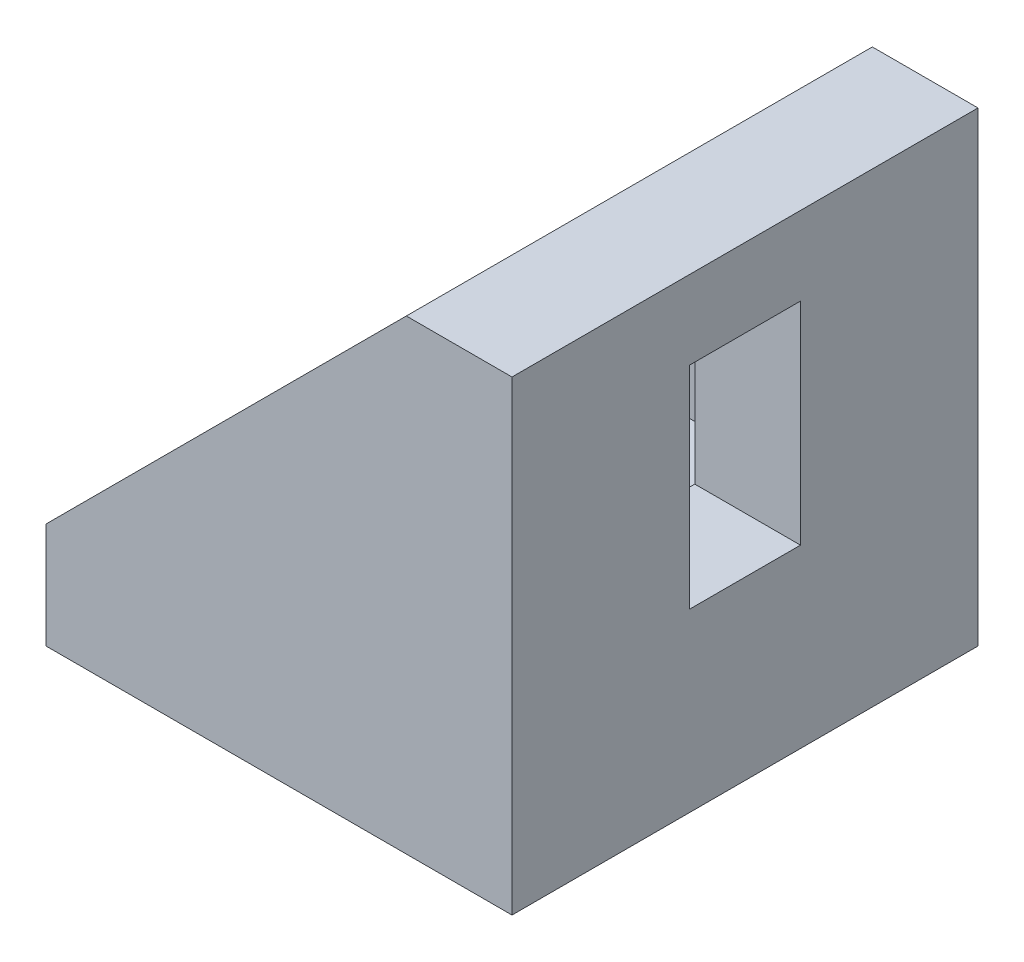
SolidWorks part; units mm, degrees
ref_plane "Front Plane" through (0, 0, 0) normal (0, 0, 1) x (1, 0, 0)
ref_plane "Top Plane" through (0, 0, 0) normal (0, 1, 0) x (1, 0, 0)
ref_plane "Right Plane" through (0, 0, 0) normal (1, 0, 0) x (0, 0, -1)
sketch "Sketch1" plane through (0, 0, 0) normal (0, 0, 1) x (1, 0, 0)
  line L0 (0, 0) -> (-42, 0)
  line L1 (-42, 0) -> (-42, 9.525)
  line L2 (-42, 9.525) -> (-9.525, 9.525)
  line L3 (-9.525, 9.525) -> (-9.525, 42)
  line L4 (-9.525, 42) -> (0, 42)
  line L5 (0, 42) -> (0, 0)
  dimension "D1" = 42
  dimension "D2" = 42
  dimension "D3" = 9.525
  dimension "D4" = 9.525
extrude "Boss-Extrude1" add sketch "Sketch1" along normal blind 21
sketch "Sketch2" plane through (0, 0, 21) normal (0, 0, 1) x (1, 0, 0)
  line L0 (-9.525, 42) -> (-42, 9.525)
  line L1 (-42, 9.525) -> (-9.525, 9.525)
  line L2 (-9.525, 9.525) -> (-42, 9.525) construction
  line L3 (-9.525, 42) -> (-9.525, 9.525) construction
  line L4 (-9.525, 9.525) -> (-9.525, 42)
extrude "Boss-Extrude2" add sketch "Sketch2" against normal blind 4.7625
mirror "Mirror1" about plane through (0, 0, 0) normal (0, 0, -1) of "Boss-Extrude2", "Boss-Extrude1"
sketch "Sketch3" plane through (0, 9.525, 0) normal (0, 1, 0) x (1, 0, 0)
  line L0 (-15.875, 0) -> (0, 0) construction
  line L1 (-15.875, 5) -> (-34.925, 5)
  line L2 (-15.875, 5) -> (-15.875, -5)
  line L3 (-15.875, -5) -> (-34.925, -5)
  line L4 (-34.925, 5) -> (-34.925, -5)
  line L5 (-9.525, -16.2375) -> (-9.525, 16.2375) construction
  dimension "D1" = 10
  dimension "D2" = 19.05
  dimension "D3" = 6.35
extrude "Cut-Extrude1" cut sketch "Sketch3" against normal through all
ref_plane "Plane1" through (0, 0, 0) normal (0.7071, 0.7071, 0) x (0, 0, -1)
mirror "Mirror2" about plane through (0, 0, 0) normal (0.7071, 0.7071, 0) of "Cut-Extrude1"
equation "\"D2@Sketch1\"=\"D1@Sketch1\""
equation "\"D4@Sketch1\"=\"D3@Sketch1\""
